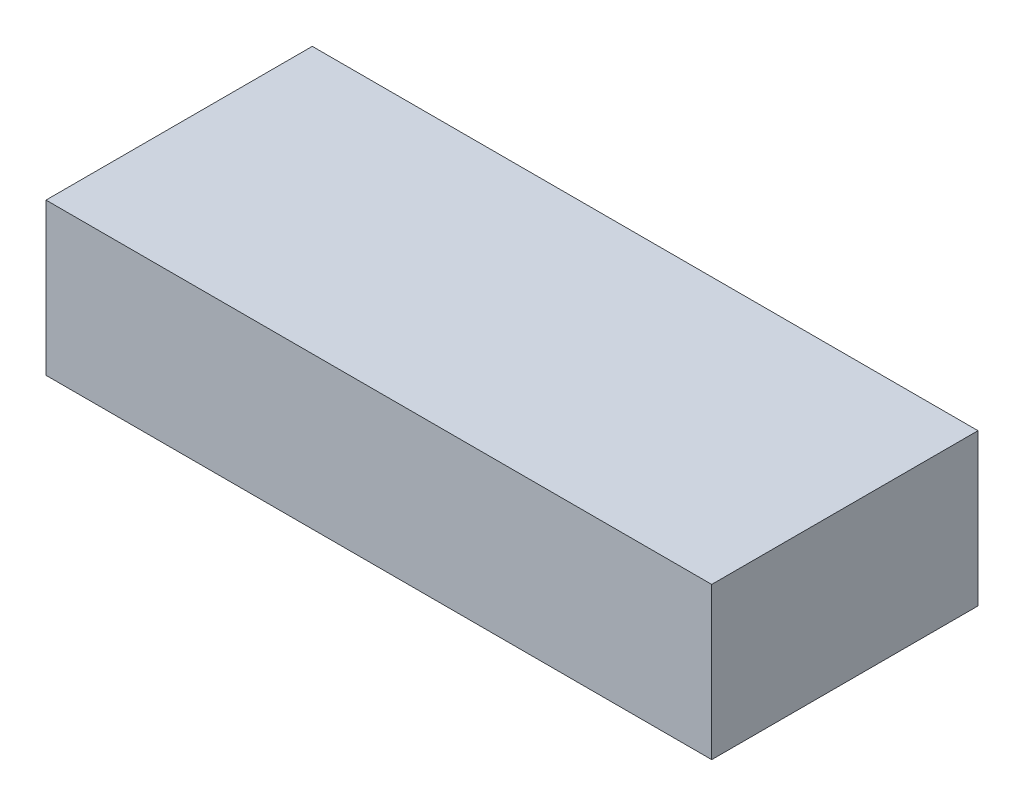
SolidWorks part; units mm, degrees
ref_plane "Front Plane" through (0, 0, 0) normal (0, 0, 1) x (1, 0, 0)
ref_plane "Top Plane" through (0, 0, 0) normal (0, 1, 0) x (1, 0, 0)
ref_plane "Right Plane" through (0, 0, 0) normal (1, 0, 0) x (0, 0, -1)
sketch "Sketch1" plane through (0, 0, 0) normal (0, 1, 0) x (1, 0, 0)
  line L1 (-12.5, 5) -> (12.5, 5)
  line L2 (-12.5, 5) -> (-12.5, -5)
  line L3 (-12.5, -5) -> (12.5, -5)
  line L4 (12.5, 5) -> (12.5, -5)
  line L5 (-12.5, 5) -> (12.5, -5) construction
  line L6 (-12.5, -5) -> (12.5, 5) construction
  point P0 (0, 0)
  dimension "D1" = 10
  dimension "D2" = 25
extrude "Boss-Extrude1" add sketch "Sketch1" along normal blind 5.7
